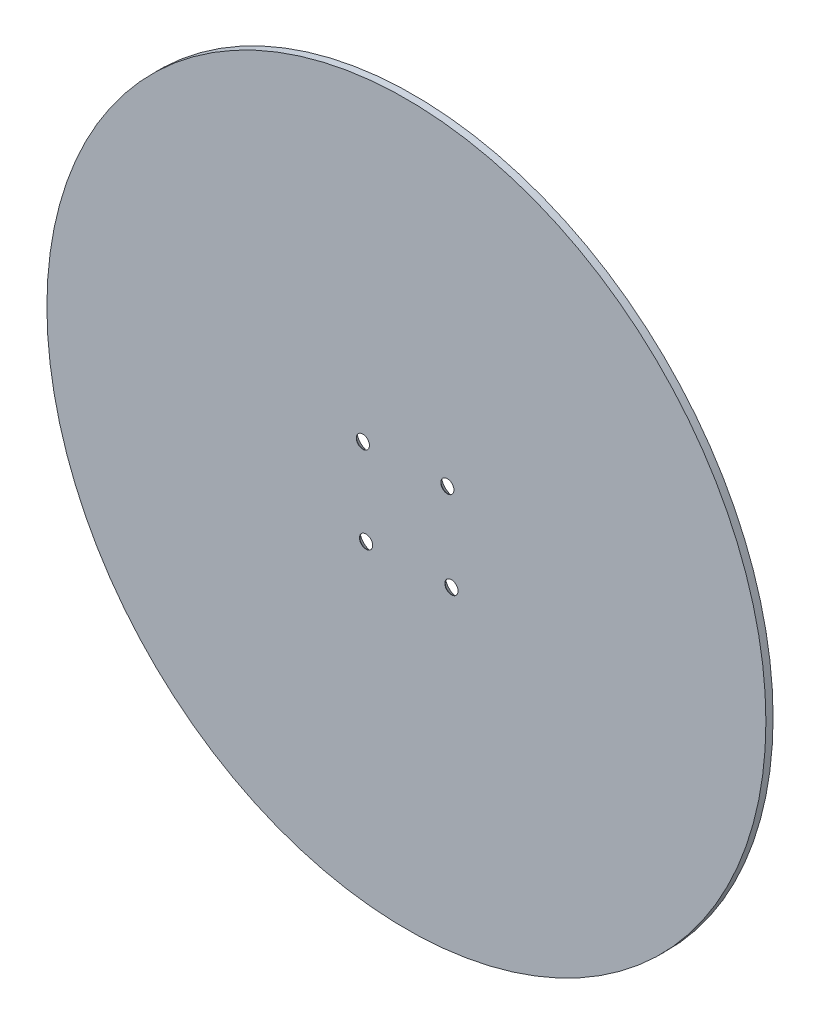
SolidWorks part; units mm, degrees
ref_plane "Front Plane" through (0, 0, 0) normal (0, 0, 1) x (1, 0, 0)
ref_plane "Top Plane" through (0, 0, 0) normal (0, 1, 0) x (1, 0, 0)
ref_plane "Right Plane" through (0, 0, 0) normal (1, 0, 0) x (0, 0, -1)
sketch "Sketch1" plane through (0, 0, 0) normal (0, 0, 1) x (1, 0, 0)
  circle A0 centre (0, 0) radius 150
  dimension "D1" = 300
extrude "Boss-Extrude1" add sketch "Sketch1" along normal blind 3 contours A0
sketch "Sketch2" plane through (0, 0, 0) normal (0, 0, -1) x (-1, 0, 0)
  circle A0 centre (16.8584, -18.4606) radius 3.2 construction
  circle A1 centre (-18.4606, -16.8584) radius 3.2 construction
  circle A2 centre (-16.8584, 18.4606) radius 3.2 construction
  circle A3 centre (16.8584, -18.4606) radius 3.2
  circle A4 centre (-18.4606, -16.8584) radius 3.2
  circle A5 centre (-16.8584, 18.4606) radius 3.2
  circle A6 centre (18.4606, 16.8584) radius 3.2 construction
  circle A7 centre (18.4606, 16.8584) radius 3.2
hole_wizard "CSK for M5 SFHCS1" positions "Sketch3" profile "Sketch4" countersink size "M5" standard "ANSI Metric" end condition through all
sketch "Sketch3" plane through (0, 0, 0) normal (0, 0, -1) x (-1, 0, 0)
  point P0 (-17.0808, 18.587)
  point P2 (18.1756, 17.0624)
  point P4 (16.8416, -18.3845)
  point P6 (-18.7959, -17.0505)
sketch "Sketch4" plane through (17.0808, 18.587, 0) normal (1, 0, 0) x (0, 1, 0)
  line L0 (0, 0) -> (0, 3)
  line L1 (0, 3) -> (2.75, 3)
  line L2 (2.75, 3) -> (2.75, 2.85)
  line L3 (2.75, 2.85) -> (5.6, 0)
  line L5 (5.6, 0) -> (0, 0)
  line L6 (-2.75, 2.85) -> (-5.6, 0) construction
  line L11 (0, -6.35) -> (0, 107.95) construction
  dimension "Thru Hole Dia." = 5.5
  dimension "Thru Hole Depth" = 3
  dimension "Near C'Sink Dia." = 11.2
  dimension "Near C'Sink Angle" = 90
